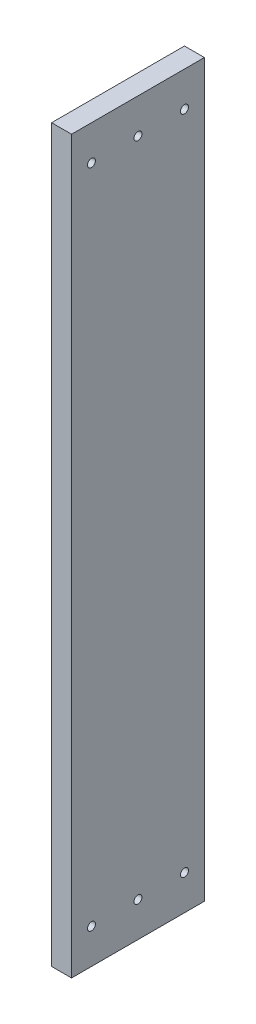
SolidWorks part; units mm, degrees
ref_plane "Front Plane" through (0, 0, 0) normal (0, 0, 1) x (1, 0, 0)
ref_plane "Top Plane" through (0, 0, 0) normal (0, 1, 0) x (1, 0, 0)
ref_plane "Right Plane" through (0, 0, 0) normal (1, 0, 0) x (0, 0, -1)
sketch "Sketch1" plane through (0, 0, 0) normal (0, 1, 0) x (1, 0, 0)
  line L1 (0, 0) -> (19.05, 0)
  line L2 (0, 0) -> (0, 127)
  line L3 (0, 127) -> (19.05, 127)
  line L4 (19.05, 0) -> (19.05, 127)
  dimension "D1" = 19.05
  dimension "D2" = 127
extrude "Boss-Extrude1" add sketch "Sketch1" along normal blind 698.5
sketch "Sketch2" plane through (19.05, 0, 0) normal (1, 0, 0) x (0, 0, -1)
  line L0 (127, 349.25) -> (0, 349.25) construction
  line L1 (127, 698.5) -> (127, 0) construction
  line L2 (0, 698.5) -> (0, 0) construction
  line L3 (0, 698.5) -> (127, 698.5) construction
  circle A0 centre (107.95, 665.226) radius 3.81
  circle A1 centre (63.5, 665.226) radius 3.81
  circle A2 centre (19.05, 665.226) radius 3.81
  circle A3 centre (19.05, 33.274) radius 3.81
  circle A4 centre (63.5, 33.274) radius 3.81
  circle A5 centre (107.95, 33.274) radius 3.81
  dimension "D1" = 7.62
  dimension "D4" = 7.62
  dimension "D5" = 7.62
  dimension "D2" = 19.05
  dimension "D3" = 33.274
  dimension "D6" = 19.05
  dimension "D7" = 44.45
  dimension "D8" = 33.274
  dimension "D9" = 33.274
extrude "Cut-Extrude1" cut sketch "Sketch2" against normal blind 67.818
equation "\"LengthOfLong\"= \"length desired@Drivetrain.SLDASM\" + 2"
equation "\"D1@Boss-Extrude1\"=\"LengthOfLong\" - 0.5"
